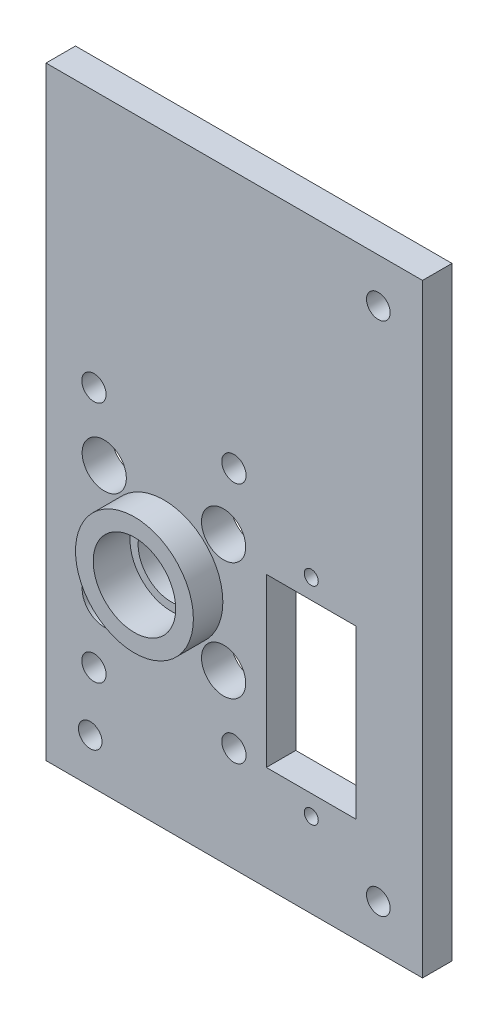
SolidWorks part; units mm, degrees
ref_plane "Front Plane" through (0, 0, 0) normal (0, 0, 1) x (1, 0, 0)
ref_plane "Top Plane" through (0, 0, 0) normal (0, 1, 0) x (1, 0, 0)
ref_plane "Right Plane" through (0, 0, 0) normal (1, 0, 0) x (0, 0, -1)
sketch "Sketch1" plane through (0, 0, 0) normal (0, 0, 1) x (1, 0, 0)
  line L0 (0, 6.2) -> (0, -16.5) construction
  line L1 (-6.1, 6.2) -> (6.1, 6.2)
  line L2 (-6.1, 6.2) -> (-6.1, -16.5)
  line L3 (-6.1, -16.5) -> (6.1, -16.5)
  line L4 (6.1, -16.5) -> (6.1, 6.2)
  line L5 (9.1, -21.65) -> (9.1, 11.35)
  line L6 (9.1, 11.35) -> (-30, 11.35)
  line L7 (-30, 11.35) -> (-30, -21.65)
  line L8 (-30, -21.65) -> (9.1, -21.65)
  circle A0 centre (0, 8.9) radius 0.95
  circle A1 centre (0, -19.2) radius 0.95
  circle A2 centre (-20, 0) radius 4.5
  point P11 (0, 6.2)
  point P16 (9.1, -5.15)
  point P17 (6.1, -5.15)
  dimension "D3" = 1.9
  dimension "D11" = 9
  dimension "D1" = 8.9
  dimension "D2" = 19.2
  dimension "D4" = 22.7
  dimension "D5" = 2.7
  dimension "D6" = 2.7
  dimension "D7" = 12.2
  dimension "D8" = 3
  dimension "D9" = 33
  dimension "D10" = 20
  dimension "D12" = 10
extrude "Boss-Extrude1" add sketch "Sketch1" along normal blind 4
sketch "Sketch2" plane through (0, 0, 0) normal (0, 0, 1) x (1, 0, 0)
  circle A0 centre (-20, 0) radius 4.4038
  circle A1 centre (-20, 0) radius 8
  dimension "D1" = 16
extrude "Boss-Extrude2" add sketch "Sketch2" along normal blind 4 from surface at 4 starting at face at (0, -5.15, 4)
sketch "Sketch3" plane through (0, 0, 0) normal (0, 0, 1) x (1, 0, 0)
  circle A0 centre (-20, 0) radius 5.6
  dimension "D1" = 11.2
extrude "Cut-Extrude1" cut sketch "Sketch3" against normal blind 5 from surface at 8 starting at face at (-12, 0, 8)
sketch "Sketch5" plane through (0, 0, 0) normal (0, 0, 1) x (1, 0, 0)
  line L0 (9.1, 11.35) -> (-30, 11.35) construction
  line L1 (-30, -21.65) -> (-36.0037, -21.65)
  line L2 (-30, -21.65) -> (-30, 21.35)
  line L3 (-30, 21.35) -> (-36.0037, 21.35)
  line L4 (-36.0037, -21.65) -> (-36.0037, 21.35)
  line L6 (-30, 21.35) -> (9.1, 21.35)
  line L7 (-30, 21.35) -> (-30, 11.35)
  line L8 (-30, 11.35) -> (9.1, 11.35)
  line L9 (9.1, 21.35) -> (9.1, 11.35)
  dimension "D1" = 10
extrude "Boss-Extrude3" add sketch "Sketch5" along normal up to surface (4 mm away) contours L9 L6 L2 L8 | L4 L1 L2 L3 up to face at (-12, 0, 4)
sketch "Sketch4" plane through (0, 0, 0) normal (0, 0, 1) x (1, 0, 0)
  line L0 (-20, 0) -> (-20, 19) construction
  line L1 (-20, 0) -> (-10.5, 16.4545) construction
  line L2 (-20, 0) -> (-1, 0) construction
  circle A0 centre (-20, 0) radius 19 construction
  circle A1 centre (-10.5, 16.4545) radius 1.65
  circle A2 centre (-29.5, 16.4545) radius 1.65
  circle A3 centre (-29.5, -16.4545) radius 1.65
  circle A4 centre (-10.5, -16.4545) radius 1.65
  dimension "D1" = 38
  dimension "D3" = 3.3
  dimension "D2" = 30
extrude "Cut-Extrude3" cut sketch "Sketch4" against normal blind 10 and the other way through all
sketch "Sketch6" plane through (0, 0, 0) normal (0, 0, 1) x (1, 0, 0)
  line L1 (-6.1, 6.2) -> (-6.1, -16.5) construction
  line L2 (-6.1, 0) -> (-20, 0) construction
  line L3 (-20, 0) -> (-20, 21.35) construction
  line L4 (-36.0037, 21.35) -> (9.1, 21.35) construction
  circle A5 centre (-11.9, 8) radius 3
  circle A6 centre (-28.1, 8) radius 3
  circle A7 centre (-11.9, -8) radius 3
  circle A8 centre (-28.1, -8) radius 3
  point P10 (0, 0)
  point P12 (-20, 8.5804)
  dimension "D1" = 8
  dimension "D3" = 6
  dimension "D2" = 8.1
extrude "Cut-Extrude4" cut sketch "Sketch6" along normal blind 10 from surface at 4
sketch "Sketch7" plane through (0, 0, 0) normal (0, 0, 1) x (1, 0, 0)
  line L0 (6.1, -16.5) -> (6.1, 6.2) construction
  line L1 (-36.0037, -21.65) -> (15.1, -21.65)
  line L2 (-36.0037, -21.65) -> (-36.0037, -30.65)
  line L3 (-36.0037, -30.65) -> (15.1, -30.65)
  line L4 (15.1, -21.65) -> (15.1, -30.65)
  line L5 (15.1, -21.65) -> (9.1, -21.65)
  line L6 (15.1, -21.65) -> (15.1, 21.35)
  line L7 (15.1, 21.35) -> (9.1, 21.35)
  line L8 (9.1, -21.65) -> (9.1, 21.35)
  line L9 (-36.0037, 21.35) -> (15.1, 21.35)
  line L10 (-36.0037, 21.35) -> (-36.0037, 51.35)
  line L11 (-36.0037, 51.35) -> (15.1, 51.35)
  line L12 (15.1, 21.35) -> (15.1, 51.35)
  dimension "D1" = 9
  dimension "D2" = 9
  dimension "D3" = 30
extrude "Boss-Extrude4" add sketch "Sketch7" along normal up to surface (4 mm away) contours L2 L1 L4 L3 | L6 L5 L8 L7 | L10 L9 L12 L11 up to face at (-25.1, 8, 4)
sketch "Sketch8" plane through (0, 0, 0) normal (0, 0, 1) x (1, 0, 0)
  line L0 (-36.0037, -30.65) -> (15.1, -30.65) construction
  line L1 (15.1, 51.35) -> (15.1, -30.65) construction
  line L2 (-36.0037, -30.65) -> (-36.0037, 51.35) construction
  line L3 (15.1, 10.35) -> (-36.0037, 10.35) construction
  circle A0 centre (9.1, -24.65) radius 1.6
  circle A1 centre (-30.0037, -24.65) radius 1.6
  circle A2 centre (9.1, 45.35) radius 1.6
  point P14 (0, 0)
  dimension "D1" = 3.2
  dimension "D6" = 3.2
  dimension "D2" = 6
  dimension "D3" = 6
  dimension "D4" = 6
  dimension "D5" = 6
extrude "Cut-Extrude6" cut sketch "Sketch8" along normal through all and the other way through all from surface
